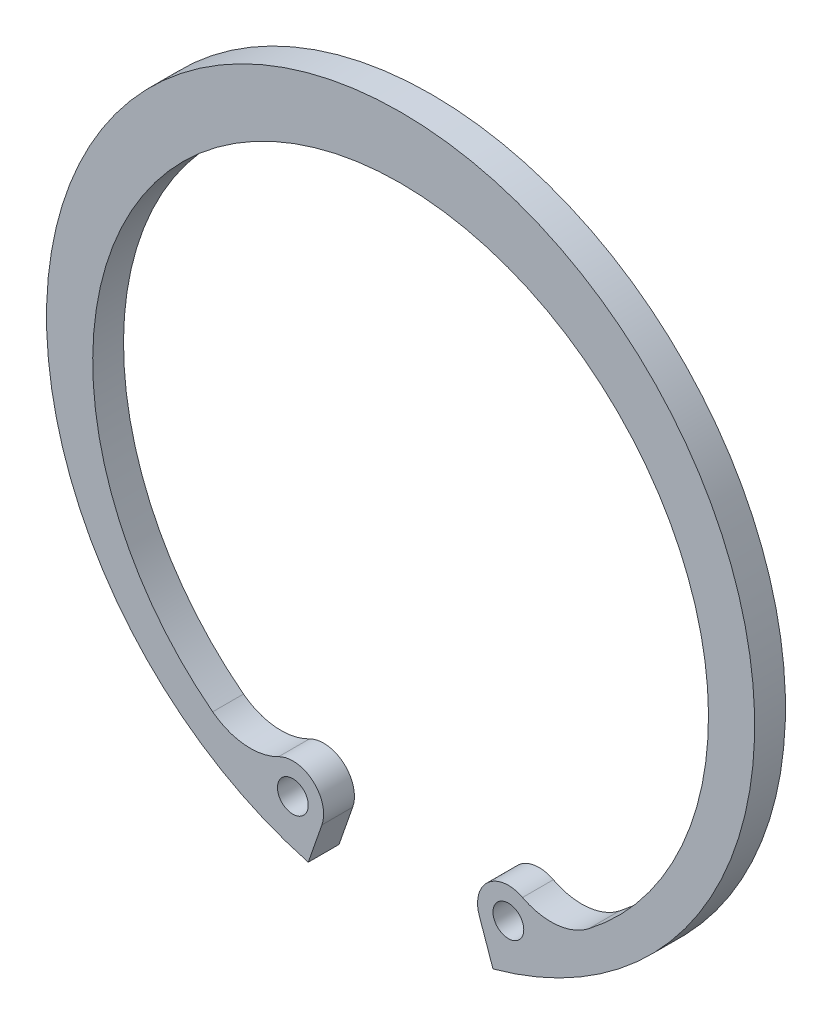
SolidWorks part; units mm, degrees
ref_plane "Front Plane" through (0, 0, 0) normal (0, 0, 1) x (1, 0, 0)
ref_plane "Top Plane" through (0, 0, 0) normal (0, 1, 0) x (1, 0, 0)
ref_plane "Right Plane" through (0, 0, 0) normal (1, 0, 0) x (0, 0, -1)
sketch "Sketch1" plane through (0, 0, 0) normal (0, 0, 1) x (1, 0, 0)
  line L5 (5.1118, -19.6592) -> (6, -22.2036)
  line L6 (-5.1118, -19.6592) -> (-6, -22.2036)
  line L8 (0, 45.6975) -> (0, -45.6975) construction
  line L9 (-7, -19) -> (7, -19)
  arc A1 (6, -22.2036) -> (-6, -22.2036) centre (0, 0) ccw
  arc A2 (12.2058, -16.8436) -> (-12.2058, -16.8436) centre (0, -1) ccw
  circle A3 centre (-7, -19) radius 1
  arc A4 (7.9215, -17.225) -> (5.1118, -19.6592) centre (7, -19) ccw
  circle A6 centre (7, -19) radius 1
  arc A7 (-5.1118, -19.6592) -> (-7.9215, -17.225) centre (-7, -19) ccw
  arc A8 (-7.9215, -17.225) -> (-12.2058, -16.8436) centre (-9.7646, -13.6749) cw
  arc A9 (12.2058, -16.8436) -> (7.9215, -17.225) centre (9.7646, -13.6749) cw
  point P3 (0, -23)
  point P5 (0, -23)
  point P16 (0, 0)
  dimension "D1" = 46
  dimension "D2" = 40
  dimension "D8" = 2
  dimension "D9" = 2
  dimension "D10" = 4
  dimension "D11" = 4
  dimension "D12" = 4
  dimension "D13" = 4
  dimension "D3" = 1
  dimension "D4" = 12
  dimension "D5" = 14
  dimension "D6" = 18
  dimension "D7" = 7
extrude "Boss-Extrude1" add sketch "Sketch1" along normal blind 2
